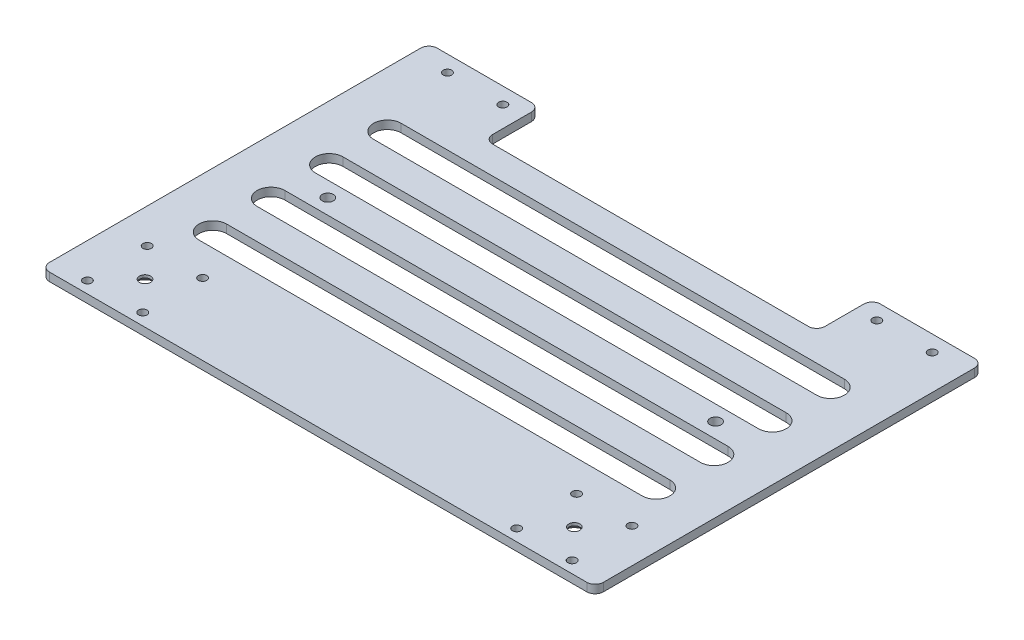
SolidWorks part; units mm, degrees
material "环氧玻璃布层压板"
ref_plane "前视基准面" through (0, 0, 0) normal (0, 0, 1) x (1, 0, 0)
ref_plane "上视基准面" through (0, 0, 0) normal (0, 1, 0) x (1, 0, 0)
ref_plane "右视基准面" through (0, 0, 0) normal (1, 0, 0) x (0, 0, -1)
other "Configuration Table"
sketch "草图1" plane through (0, 0, 0) normal (0, 1, 0) x (1, 0, 0)
  line L1 (-100, 60) -> (100, 60)
  line L2 (-100, 60) -> (-100, -60)
  line L3 (-100, -60) -> (100, -60)
  line L4 (100, 60) -> (100, -60)
  line L5 (0, -60) -> (0, 60) construction
  line L6 (-100, 0) -> (100, 0) construction
  point P0 (0, 0)
  dimension "D1" = 120
  dimension "D2" = 200
extrude "凸台-拉伸1" add sketch "草图1" along normal blind 3
sketch "草图2" plane through (0, 3, 0) normal (0, 1, 0) x (1, 0, 0)
  line L0 (0, 0) -> (0, 69.5653) construction
  circle A0 centre (67.5, 54.2) radius 1.525 construction
  circle A1 centre (87.5, 54.2) radius 1.525 construction
  circle A2 centre (67.5, -54.2) radius 1.525 construction
  circle A3 centre (87.5, -54.2) radius 1.525 construction
  circle A4 centre (67.5, 54.2) radius 1.525
  circle A5 centre (87.5, 54.2) radius 1.525
  circle A6 centre (67.5, -54.2) radius 1.525
  circle A7 centre (87.5, -54.2) radius 1.525
  circle A8 centre (-87.5, -54.2) radius 1.525
  circle A9 centre (-67.5, -54.2) radius 1.525
  circle A10 centre (-87.5, 54.2) radius 1.525
  circle A11 centre (-67.5, 54.2) radius 1.525
extrude "切除-拉伸1" cut sketch "草图2" against normal blind 3
sketch "草图3" plane through (0, 3, 0) normal (0, 1, 0) x (1, 0, 0)
  line L0 (100, 60) -> (-100, 60) construction
  line L1 (-60, 80) -> (60, 80)
  line L2 (-60, 80) -> (-60, 40)
  line L3 (-60, 40) -> (60, 40)
  line L4 (60, 80) -> (60, 40)
  line L5 (0, 40) -> (0, 80) construction
  line L6 (-60, 60) -> (60, 60) construction
  point P0 (0, 60)
  dimension "D1" = 20
  dimension "D2" = 120
extrude "切除-拉伸2" cut sketch "草图3" against normal blind 3
sketch "草图4" plane through (0, 3, 0) normal (0, 1, 0) x (1, 0, 0)
  line L0 (0, 0) -> (0, 40) construction
  line L1 (-60, 40) -> (60, 40) construction
  line L2 (-80, 25) -> (80, 25) construction
  line L3 (-80, 30) -> (80, 30)
  line L4 (-80, 20) -> (80, 20)
  line L5 (-80, 4) -> (80, 4) construction
  line L6 (-80, 9) -> (80, 9)
  line L7 (-80, -1) -> (80, -1)
  line L8 (-80, -17) -> (80, -17) construction
  line L9 (-80, -12) -> (80, -12)
  line L10 (-80, -22) -> (80, -22)
  line L11 (-80, -38) -> (80, -38) construction
  line L12 (-80, -33) -> (80, -33)
  line L13 (-80, -43) -> (80, -43)
  arc A0 (-80, 30) -> (-80, 20) centre (-80, 25) ccw
  arc A1 (80, 20) -> (80, 30) centre (80, 25) ccw
  arc A2 (-80, 9) -> (-80, -1) centre (-80, 4) ccw
  arc A3 (80, -1) -> (80, 9) centre (80, 4) ccw
  arc A4 (-80, -12) -> (-80, -22) centre (-80, -17) ccw
  arc A5 (80, -22) -> (80, -12) centre (80, -17) ccw
  arc A6 (-80, -33) -> (-80, -43) centre (-80, -38) ccw
  arc A7 (80, -43) -> (80, -33) centre (80, -38) ccw
  point P7 (0, 25)
  point P16 (0, 4)
  point P23 (0, -17)
  point P30 (0, -38)
  dimension "D1" = 5
  dimension "D2" = 160
  dimension "D3" = 10
  dimension "D5" = 21
  dimension "D4" = 4
extrude "切除-拉伸3" cut sketch "草图4" against normal blind 10
sketch "草图5" plane through (0, 3, 0) normal (0, 1, 0) x (1, 0, 0)
  line L0 (100, -60) -> (100, 60) construction
  line L1 (-100, -60) -> (100, -60)
  line L2 (-100, -60) -> (-100, -80)
  line L3 (-100, -80) -> (100, -80)
  line L4 (100, -60) -> (100, -80)
  dimension "D1" = 20
extrude "凸台-拉伸2" add sketch "草图5" against normal up to surface (3 mm away) up to face at (0, 0, -25)
sketch "草图7" plane through (0, 3, 0) normal (0, 1, 0) x (1, 0, 0)
  line L0 (-100, -80) -> (100, -80) construction
  line L1 (-100, 60) -> (-100, -80) construction
  circle A0 centre (-87.5, -75.8) radius 1.525
  circle A1 centre (-67.5, -75.8) radius 1.525
  dimension "D1" = 20
  dimension "D2" = 4.2
  dimension "D4" = 3.05
  dimension "D3" = 12.5
extrude "切除-拉伸4" cut sketch "草图7" against normal through all
mirror "镜向1" about plane through (0, 0, 0) normal (1, 0, 0) of "切除-拉伸4"
sketch "草图9" plane through (0, 3, 0) normal (0, 1, 0) x (1, 0, 0)
  line L0 (-87.5, -54.2) -> (-87.5, -75.8) construction
  line L1 (-87.5, -75.8) -> (-67.5, -75.8) construction
  point P3 (-77.5, -65)
  point P8 (-77.5, -75.8)
  point P9 (-87.5, -65)
hole_wizard "孔2" positions "草图11" profile "草图12" legacy end condition through all
sketch "草图11" plane through (0, 0, 0) normal (0, -1, 0) x (-1, 0, 0)
  point P0 (77.5, -65)
sketch "草图12" plane through (-77.5, 0, 65) normal (1, 0, 0) x (0, 0, -1)
  line L0 (0, 0) -> (0, 3)
  line L1 (0, 3) -> (2, 3)
  line L2 (2, 3) -> (2, 2)
  line L3 (2, 2) -> (4, 0)
  line L4 (4, 0) -> (0, 0)
  line L5 (0, -6.4453) -> (0, 115.525) construction
  line L6 (-2, 2) -> (-4, 0) construction
  dimension "直径" = 4
  dimension "深度" = 3
  dimension "锥坑角度" = 90
  dimension "锥坑直径" = 8
mirror "镜向3" about plane through (0, 0, 0) normal (1, 0, 0) of "孔2"
sketch "草图14" plane through (0, 0, 0) normal (0, -1, 0) x (1, 0, 0)
  line L0 (-80, 12) -> (-80, 1) construction
  line L1 (-100, -60) -> (-100, 80) construction
  circle A0 centre (-70, 6.5) radius 2.025
  point P6 (-80, 6.5)
  dimension "D1" = 4.05
  dimension "D2" = 30
extrude "切除-拉伸5" cut sketch "草图14" against normal through all
mirror "镜向4" about plane through (0, 0, 0) normal (1, 0, 0) of "切除-拉伸5"
sketch "草图15" plane through (0, 0, 0) normal (0, -1, 0) x (1, 0, 0)
  line L1 (0, 22) -> (0, 33) construction
  line L2 (-80, 22) -> (80, 22) construction
  line L3 (80, 33) -> (-80, 33) construction
  circle A0 centre (0, 27.5) radius 2.025
  dimension "D1" = 4.05
extrude "切除-拉伸6" cut sketch "草图15" against normal through all
fillet "圆角1" radius 3 8 edges at (-60, 1.5, -40) (-60, 1.5, -60) (-100, 1.5, -60) (100, 1.5, 80) (100, 1.5, -60) (60, 1.5, -60) (60, 1.5, -40) (-100, 1.5, 80)
